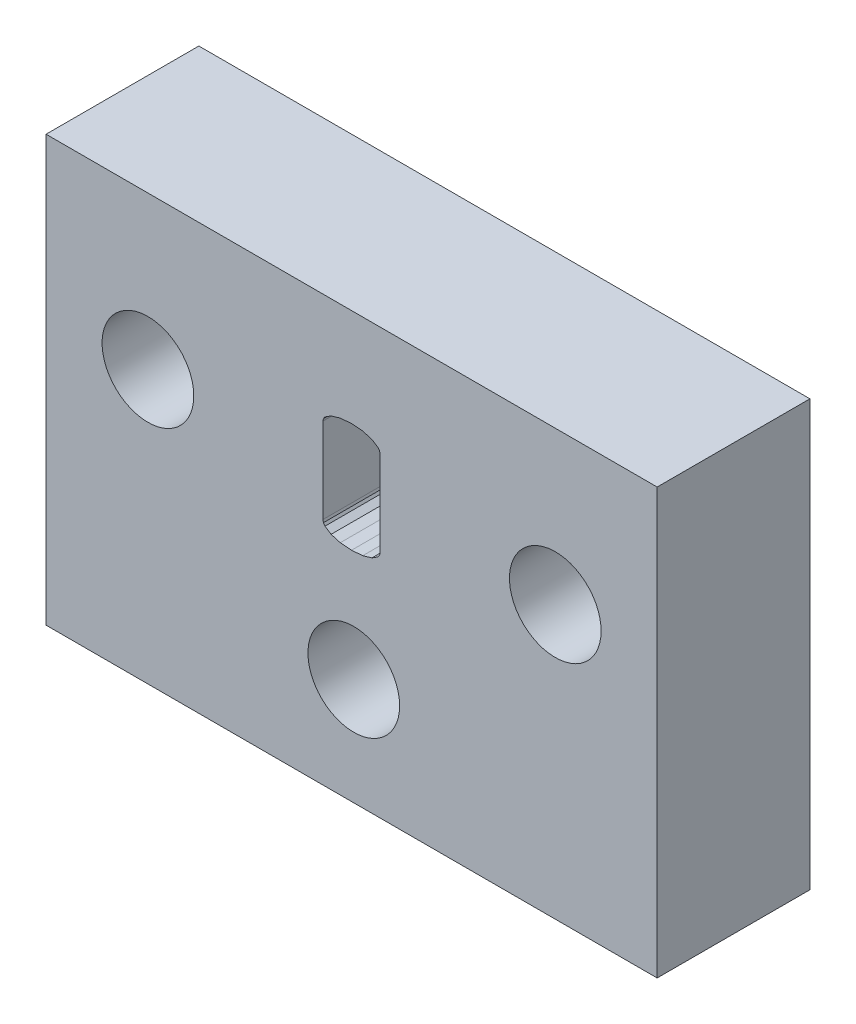
SolidWorks part; units mm, degrees
ref_plane "Plano frontal" through (0, 0, 0) normal (0, 0, 1) x (1, 0, 0)
ref_plane "Plano superior" through (0, 0, 0) normal (0, 1, 0) x (1, 0, 0)
ref_plane "Plano direito" through (0, 0, 0) normal (1, 0, 0) x (0, 0, -1)
sketch "Model" plane through (0, 0, 0) normal (0, 0, 1) x (1, 0, 0)
  line L0 (31.7767, 24.0536) -> (55.7767, 24.0536)
  line L1 (31.7767, 7.3536) -> (31.7767, 24.0536)
  line L2 (55.7767, 24.0536) -> (55.7767, 7.3536)
  line L3 (55.7767, 7.3536) -> (31.7767, 7.3536)
  line L4 (42.6491, 16.3825) -> (42.6692, 16.2863)
  line L5 (42.6692, 16.2863) -> (42.7295, 16.1975)
  line L6 (42.7295, 16.1975) -> (42.9707, 16.0422)
  line L7 (42.9707, 16.0422) -> (43.3321, 15.9369)
  line L8 (43.3321, 15.9369) -> (43.773, 15.9018)
  line L9 (43.773, 15.9018) -> (44.214, 15.9369)
  line L10 (44.214, 15.9369) -> (44.5754, 16.0422)
  line L11 (44.5754, 16.0422) -> (44.8166, 16.1975)
  line L12 (44.8166, 16.1975) -> (44.8769, 16.2863)
  line L13 (44.8769, 16.2863) -> (44.897, 16.3825)
  line L14 (44.897, 16.3825) -> (44.897, 19.7289)
  line L15 (44.897, 19.7289) -> (44.8769, 19.8251)
  line L16 (44.8769, 19.8251) -> (44.8166, 19.9139)
  line L17 (44.8166, 19.9139) -> (44.5754, 20.0692)
  line L18 (44.5754, 20.0692) -> (44.214, 20.1746)
  line L19 (44.214, 20.1746) -> (43.773, 20.2097)
  line L20 (43.773, 20.2097) -> (43.3321, 20.1746)
  line L21 (43.3321, 20.1746) -> (42.9707, 20.0692)
  line L22 (42.9707, 20.0692) -> (42.7295, 19.9139)
  line L23 (42.7295, 19.9139) -> (42.6692, 19.8251)
  line L24 (42.6692, 19.8251) -> (42.6491, 19.7289)
  line L25 (42.6491, 19.7289) -> (42.6491, 16.3825)
  line L26 (44.897, 16.3825) -> (44.8769, 16.2863)
  line L27 (44.8769, 16.2863) -> (44.8166, 16.1975)
  line L28 (44.8166, 16.1975) -> (44.5754, 16.0422)
  line L29 (44.5754, 16.0422) -> (44.214, 15.9369)
  line L30 (44.214, 15.9369) -> (43.773, 15.9018)
  line L31 (43.773, 15.9018) -> (43.3321, 15.9369)
  line L32 (43.3321, 15.9369) -> (42.9707, 16.0422)
  line L33 (42.9707, 16.0422) -> (42.7295, 16.1975)
  line L34 (42.7295, 16.1975) -> (42.6692, 16.2863)
  line L35 (42.6692, 16.2863) -> (42.6491, 16.3825)
  line L36 (42.6491, 16.3825) -> (42.6491, 19.7289)
  line L37 (42.6491, 19.7289) -> (42.6692, 19.8251)
  line L38 (42.6692, 19.8251) -> (42.7295, 19.9139)
  line L39 (42.7295, 19.9139) -> (42.9707, 20.0692)
  line L40 (42.9707, 20.0692) -> (43.3321, 20.1746)
  line L41 (43.3321, 20.1746) -> (43.773, 20.2097)
  line L42 (43.773, 20.2097) -> (44.214, 20.1746)
  line L43 (44.214, 20.1746) -> (44.5754, 20.0692)
  line L44 (44.5754, 20.0692) -> (44.8166, 19.9139)
  line L45 (44.8166, 19.9139) -> (44.8769, 19.8251)
  line L46 (44.8769, 19.8251) -> (44.897, 19.7289)
  line L47 (44.897, 19.7289) -> (44.897, 16.3825)
  circle A0 centre (51.7756, 18.0536) radius 1.8
  circle A1 centre (43.8614, 11.5536) radius 1.8
  circle A2 centre (35.7767, 18.0536) radius 1.8
extrude "Ressalto-extrusão1" add sketch "Model" along normal blind 6 contours L3 L2 L0 L1 A2 A1 A0 L25 L24 L23 L22 L21 L20 L19 L18 L17 L16 L15 L14 L13 L12 L11 L10 L9 L8 L7 L6 L5 L4
